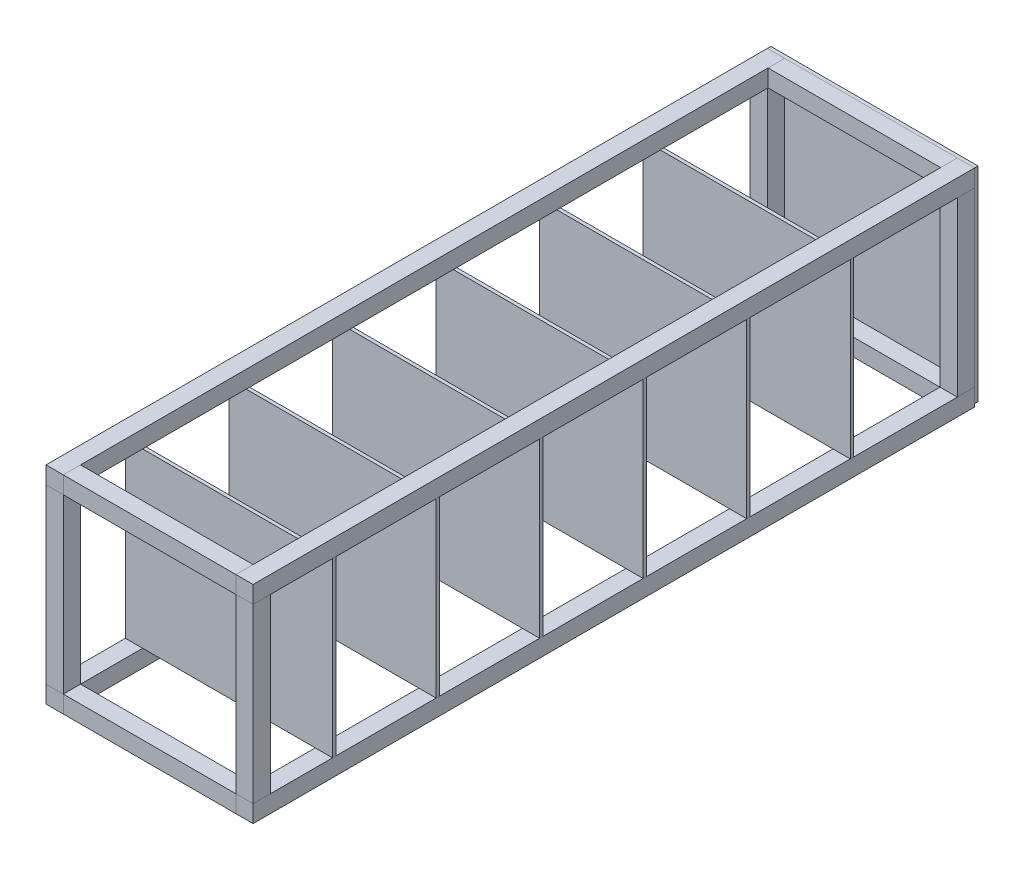
SolidWorks part; units mm, degrees
ref_plane "Front Plane" through (0, 0, 0) normal (0, 0, 1) x (1, 0, 0)
ref_plane "Top Plane" through (0, 0, 0) normal (0, 1, 0) x (1, 0, 0)
ref_plane "Right Plane" through (0, 0, 0) normal (1, 0, 0) x (0, 0, -1)
sketch "Sketch1" plane through (0, 0, 0) normal (0, 0, 1) x (1, 0, 0)
  line L0 (-550, 550) -> (-600, 550)
  line L1 (0, 0) -> (-50, 0)
  line L2 (0, 0) -> (0, -50)
  line L3 (0, -50) -> (-50, -50)
  line L4 (-50, 0) -> (-50, -50)
  line L5 (-550, 550) -> (-550, 500)
  line L6 (-550, 500) -> (-600, 500)
  line L7 (-600, 550) -> (-600, 500)
  line L8 (-550, 0) -> (-600, 0)
  line L9 (-550, 0) -> (-550, -50)
  line L10 (-550, -50) -> (-600, -50)
  line L11 (-600, 0) -> (-600, -50)
  line L12 (0, 550) -> (-50, 550)
  line L13 (0, 550) -> (0, 500)
  line L14 (0, 500) -> (-50, 500)
  line L15 (-50, 550) -> (-50, 500)
  dimension "D1" = 50
  dimension "D2" = 50
  dimension "D3" = 50
  dimension "D4" = 50
  dimension "D5" = 50
  dimension "D6" = 50
  dimension "D7" = 50
  dimension "D8" = 50
  dimension "D9" = 500
  dimension "D10" = 600
extrude "Boss-Extrude1" add sketch "Sketch1" along normal blind 2090
sketch "Sketch2" plane through (0, 0, 0) normal (0, 1, 0) x (1, 0, 0)
  line L0 (-550, -2090) -> (-550, 0) construction
  line L1 (-600, 0) -> (-550, 0)
  line L2 (-600, 0) -> (-600, -50)
  line L3 (-600, -50) -> (-550, -50)
  line L4 (-550, 0) -> (-550, -50)
  line L5 (0, 0) -> (-50, 0)
  line L6 (0, 0) -> (0, -50)
  line L7 (0, -50) -> (-50, -50)
  line L8 (-50, 0) -> (-50, -50)
  line L9 (-50, -2090) -> (-50, 0) construction
  line L10 (0, -2090) -> (0, 0) construction
  line L11 (-550, -2090) -> (-600, -2090) construction
  line L12 (-600, -2090) -> (-550, -2090)
  line L13 (-600, -2090) -> (-600, -2040)
  line L14 (-600, -2040) -> (-550, -2040)
  line L15 (-550, -2090) -> (-550, -2040)
  line L16 (-600, -2090) -> (-600, 0) construction
  line L18 (-50, -2090) -> (0, -2090)
  line L19 (-50, -2090) -> (-50, -2040)
  line L20 (-50, -2040) -> (0, -2040)
  line L21 (0, -2090) -> (0, -2040)
  dimension "D1" = 50
  dimension "D2" = 50
  dimension "D3" = 50
extrude "Boss-Extrude2" add sketch "Sketch2" along normal up to surface (500 mm away) separate body up to face at (-575, 500, 1045)
sketch "Sketch3" plane through (-550, 0, 0) normal (1, 0, 0) x (0, 0, -1)
  line L0 (-2090, -50) -> (0, -50) construction
  line L1 (-2090, 550) -> (-2040, 550)
  line L2 (-2090, 550) -> (-2090, 500)
  line L3 (-2090, 500) -> (-2040, 500)
  line L4 (-2040, 550) -> (-2040, 500)
  line L5 (-2090, 0) -> (-2040, 0)
  line L6 (-2090, 0) -> (-2090, -50)
  line L7 (-2090, -50) -> (-2040, -50)
  line L8 (-2040, 0) -> (-2040, -50)
  line L10 (0, 500) -> (-48.2707, 500)
  line L11 (0, 500) -> (0, 550)
  line L12 (0, 550) -> (-48.2707, 550)
  line L13 (-48.2707, 500) -> (-48.2707, 550)
  line L14 (-50, 0) -> (0, 0)
  line L15 (-50, 0) -> (-50, -50)
  line L16 (-50, -50) -> (0, -50)
  line L17 (0, 0) -> (0, -50)
extrude "Boss-Extrude3" add sketch "Sketch3" along normal up to surface (500 mm away) separate body up to face at (-50, 250, 25)
sketch "Sketch5" plane through (-600, 0, 0) normal (-1, 0, 0) x (0, 0, 1)
  line L0 (2090, 0) -> (0, 0) construction
  line L1 (350, 0) -> (360, 0)
  line L2 (350, 0) -> (350, 500)
  line L3 (350, 500) -> (360, 500)
  line L4 (360, 0) -> (360, 500)
  line L5 (2090, 500) -> (0, 500) construction
  line L6 (50, 500) -> (50, 0) construction
  line L7 (650, 0) -> (660, 0)
  line L8 (650, 0) -> (650, 500)
  line L9 (650, 500) -> (660, 500)
  line L10 (660, 0) -> (660, 500)
  line L11 (950, 0) -> (960, 0)
  line L12 (950, 0) -> (950, 500)
  line L13 (950, 500) -> (960, 500)
  line L14 (960, 0) -> (960, 500)
  line L15 (1250, 0) -> (1260, 0)
  line L16 (1250, 0) -> (1250, 500)
  line L17 (1250, 500) -> (1260, 500)
  line L18 (1260, 0) -> (1260, 500)
  line L19 (1550, 0) -> (1560, 0)
  line L20 (1550, 0) -> (1550, 500)
  line L21 (1550, 500) -> (1560, 500)
  line L22 (1560, 0) -> (1560, 500)
  line L23 (1850, 0) -> (1860, 0)
  line L24 (1850, 0) -> (1850, 500)
  line L25 (1850, 500) -> (1860, 500)
  line L26 (1860, 0) -> (1860, 500)
  dimension "D1" = 10
  dimension "D2" = 300
  dimension "D3" = 6
extrude "Boss-Extrude4" add sketch "Sketch5" against normal up to surface (600 mm away) separate body up to face at (0, -25, 1045)
sketch "Sketch6" plane through (0, 0, 0) normal (0, 0, -1) x (-1, 0, 0)
  line L0 (0, -50) -> (0, 0) construction
  line L1 (600, 550) -> (0, 550)
  line L2 (600, 550) -> (600, -41.2746)
  line L3 (600, -41.2746) -> (0, -41.2746)
  line L4 (0, 550) -> (0, -41.2746)
extrude "Boss-Extrude5" add sketch "Sketch6" along normal blind 10 separate body
equation "\"DD\"=50"
equation "\"D1@Sketch1\"=\"DD\""
equation "\"D2@Sketch1\"=\"DD\""
equation "\"D1@Sketch2\"=\"DD\""
equation "\"D3@Sketch2\"=\"DD\""
